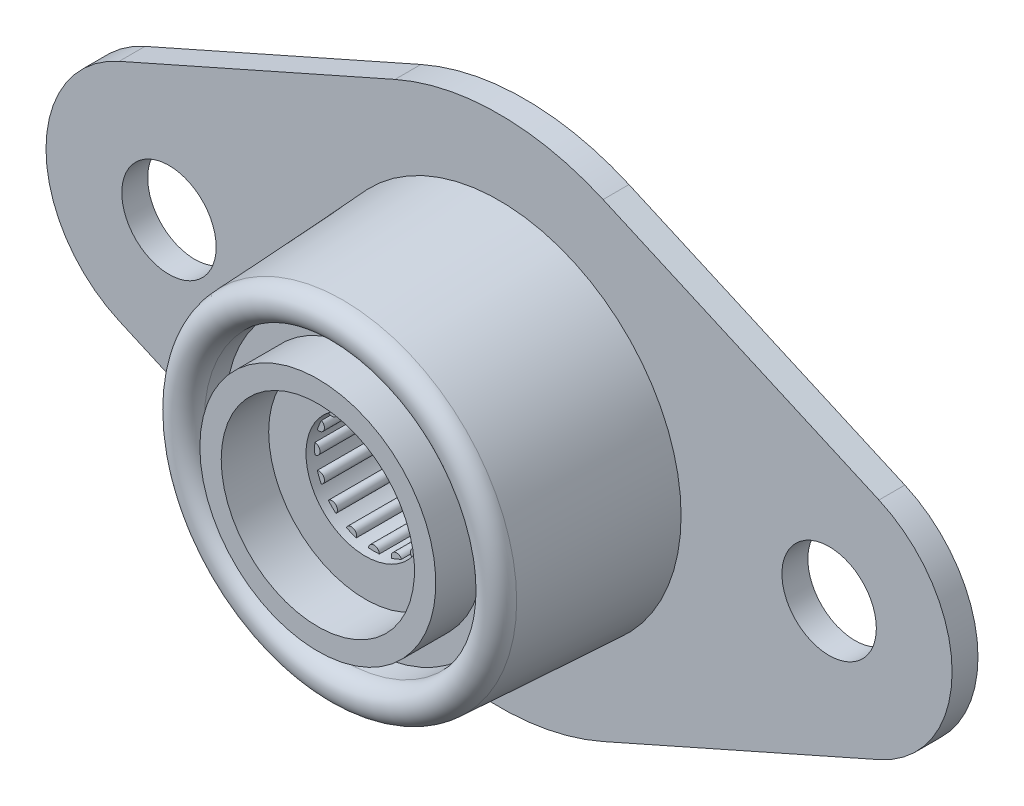
SolidWorks part; units mm, degrees
ref_plane "Front" through (0, 0, 0) normal (0, 0, 1) x (1, 0, 0)
ref_plane "Top" through (0, 0, 0) normal (0, 1, 0) x (1, 0, 0)
ref_plane "Right" through (0, 0, 0) normal (1, 0, 0) x (0, 0, -1)
sketch "Sketch1" plane through (0, 0, 0) normal (0, 0, 1) x (1, 0, 0)
  line L0 (0, 0) -> (-19.431, 0) construction
  line L1 (0, 0) -> (19.431, 0) construction
  line L2 (-22.3645, 6.618) -> (-6.1242, 13.8165)
  line L3 (6.1242, 13.8165) -> (22.3645, 6.618)
  line L4 (22.3645, -6.618) -> (6.1242, -13.8165)
  line L5 (-6.1242, -13.8165) -> (-22.3645, -6.618)
  arc A0 (6.1242, 13.8165) -> (-6.1242, 13.8165) centre (0, 0) ccw
  circle A1 centre (-19.431, 0) radius 2.7781
  circle A2 centre (19.431, 0) radius 2.7781
  arc A3 (22.3645, -6.618) -> (22.3645, 6.618) centre (19.431, 0) ccw
  arc A4 (-22.3645, 6.618) -> (-22.3645, -6.618) centre (-19.431, 0) ccw
  circle A5 centre (0, 0) radius 10.7156
  arc A7 (-6.1242, -13.8165) -> (6.1242, -13.8165) centre (0, 0) ccw
  dimension "H" = 5.5562
  dimension "C" = 30.226
  dimension "A" = 21.4312
  dimension "B" = 53.34
  dimension "D" = 38.862
extrude "Extrude1" add sketch "Sketch1" along normal blind 1.524
sketch "Sketch2" plane through (0, 0, 0) normal (1, 0, 0) x (0, 0, -1)
  line L0 (0, 10.7156) -> (-1.524, 10.7156)
  line L1 (-1.524, 10.7156) -> (-10.7205, 10.2337)
  line L2 (-10.6673, 8.2017) -> (-9.3973, 8.2017)
  line L3 (-9.3973, 8.2017) -> (-9.3973, 6.945)
  line L4 (-9.3973, 3.175) -> (0, 3.175)
  line L5 (0, 3.175) -> (0, 10.7156)
  line L6 (-9.3973, 6.945) -> (-12.192, 6.945)
  line L7 (-12.192, 6.945) -> (-12.192, 5.6883)
  line L8 (-12.192, 5.6883) -> (-9.3973, 5.6883)
  line L9 (-9.3973, 6.945) -> (-9.3973, 5.6883) construction
  line L10 (0, 0) -> (-9.3973, 0) construction
  line L11 (-9.3973, 0) -> (-9.3973, 3.175) construction
  line L12 (-9.3973, 4.4317) -> (-9.3973, 3.175)
  line L13 (-9.3973, 5.6883) -> (-9.3973, 4.4317)
  line L14 (0, 13.8165) -> (0, 15.113) construction
  line L15 (0, 13.8165) -> (0, 15.113) construction
  line L16 (-10.6673, 9.2184) -> (-11.684, 9.2184) construction
  arc A0 (-10.7205, 10.2337) -> (-11.684, 9.2184) centre (-10.6673, 9.2184) ccw
  arc A1 (-11.684, 9.2184) -> (-10.6673, 8.2017) centre (-10.6673, 9.2184) ccw
  dimension "D1" = 11.684
  dimension "F" = 11.684
  dimension "Shaft Dia" = 6.35
  dimension "D3" = 2.032
  dimension "D4" = 1.27
  dimension "D5" = 3
  dimension "G" = 12.192
revolve "Revolve1" add sketch "Sketch2" angle 360 about L10
sketch "Sketch3" plane through (0, 0, 9.3973) normal (0, 0, 1) x (1, 0, 0)
  line L0 (0, 0) -> (3.4925, 0) construction
  arc A0 (-1.624, 3.0919) -> (-2.2351, 2.6836) centre (0, 0) ccw
  arc A1 (3.4781, 0.3172) -> (3.4781, -0.3172) centre (3.4925, 0) ccw
  circle A2 centre (0, 0) radius 3.175 construction
  arc A3 (3.3347, -1.038) -> (3.0919, -1.624) centre (3.2266, -1.3365) ccw
  arc A4 (2.6836, -2.2351) -> (2.2351, -2.6836) centre (2.4696, -2.4696) ccw
  arc A5 (1.624, -3.0919) -> (1.038, -3.3347) centre (1.3365, -3.2266) ccw
  arc A6 (0.3172, -3.4781) -> (-0.3172, -3.4781) centre (0, -3.4925) ccw
  arc A7 (-1.038, -3.3347) -> (-1.624, -3.0919) centre (-1.3365, -3.2266) ccw
  arc A8 (-2.2351, -2.6836) -> (-2.6836, -2.2351) centre (-2.4696, -2.4696) ccw
  arc A9 (-3.0919, -1.624) -> (-3.3347, -1.038) centre (-3.2266, -1.3365) ccw
  arc A10 (-3.4781, -0.3172) -> (-3.4781, 0.3172) centre (-3.4925, 0) ccw
  arc A11 (-3.3347, 1.038) -> (-3.0919, 1.624) centre (-3.2266, 1.3365) ccw
  arc A12 (-2.6836, 2.2351) -> (-2.2351, 2.6836) centre (-2.4696, 2.4696) ccw
  arc A13 (-1.624, 3.0919) -> (-1.038, 3.3347) centre (-1.3365, 3.2266) ccw
  arc A14 (-0.3172, 3.4781) -> (0.3172, 3.4781) centre (0, 3.4925) ccw
  arc A15 (1.038, 3.3347) -> (1.624, 3.0919) centre (1.3365, 3.2266) ccw
  arc A16 (2.2351, 2.6836) -> (2.6836, 2.2351) centre (2.4696, 2.4696) ccw
  arc A17 (3.0919, 1.624) -> (3.3347, 1.038) centre (3.2266, 1.3365) ccw
  arc A18 (-2.6836, 2.2351) -> (-3.0919, 1.624) centre (0, 0) ccw
  arc A19 (-3.3347, 1.038) -> (-3.4781, 0.3172) centre (0, 0) ccw
  arc A20 (-3.4781, -0.3172) -> (-3.3347, -1.038) centre (0, 0) ccw
  arc A21 (-3.0919, -1.624) -> (-2.6836, -2.2351) centre (0, 0) ccw
  arc A22 (-2.2351, -2.6836) -> (-1.624, -3.0919) centre (0, 0) ccw
  arc A23 (-1.038, -3.3347) -> (-0.3172, -3.4781) centre (0, 0) ccw
  arc A24 (0.3172, -3.4781) -> (1.038, -3.3347) centre (0, 0) ccw
  arc A25 (1.624, -3.0919) -> (2.2351, -2.6836) centre (0, 0) ccw
  arc A26 (2.6836, -2.2351) -> (3.0919, -1.624) centre (0, 0) ccw
  arc A27 (3.3347, -1.038) -> (3.4781, -0.3172) centre (0, 0) ccw
  arc A28 (3.4781, 0.3172) -> (3.3347, 1.038) centre (0, 0) ccw
  arc A29 (3.0919, 1.624) -> (2.6836, 2.2351) centre (0, 0) ccw
  arc A30 (2.2351, 2.6836) -> (1.624, 3.0919) centre (0, 0) ccw
  arc A31 (1.038, 3.3347) -> (0.3172, 3.4781) centre (0, 0) ccw
  arc A32 (-0.3172, 3.4781) -> (-1.038, 3.3347) centre (0, 0) ccw
  dimension "D1" = 6.985
extrude "Cut-Extrude2" cut sketch "Sketch3" against normal through all
sketch "Sketch4" plane through (0, 0, 9.3973) normal (0, 0, 1) x (1, 0, 0)
  circle A0 centre (0, 0) radius 3.4925
extrude "Cut-Extrude3" cut sketch "Sketch4" against normal blind 0.508
sketch "Sketch5" plane through (0, 0, 0) normal (0, 0, -1) x (-1, 0, 0)
  circle A0 centre (0, 0) radius 3.4925
  arc A1 (1.038, 3.3347) -> (0.3172, 3.4781) centre (0, 0) ccw construction
extrude "Cut-Extrude4" cut sketch "Sketch5" against normal blind 0.508
equation "\"D1@Sketch3\"=\"Shaft Dia@Sketch2\"*1.1"
